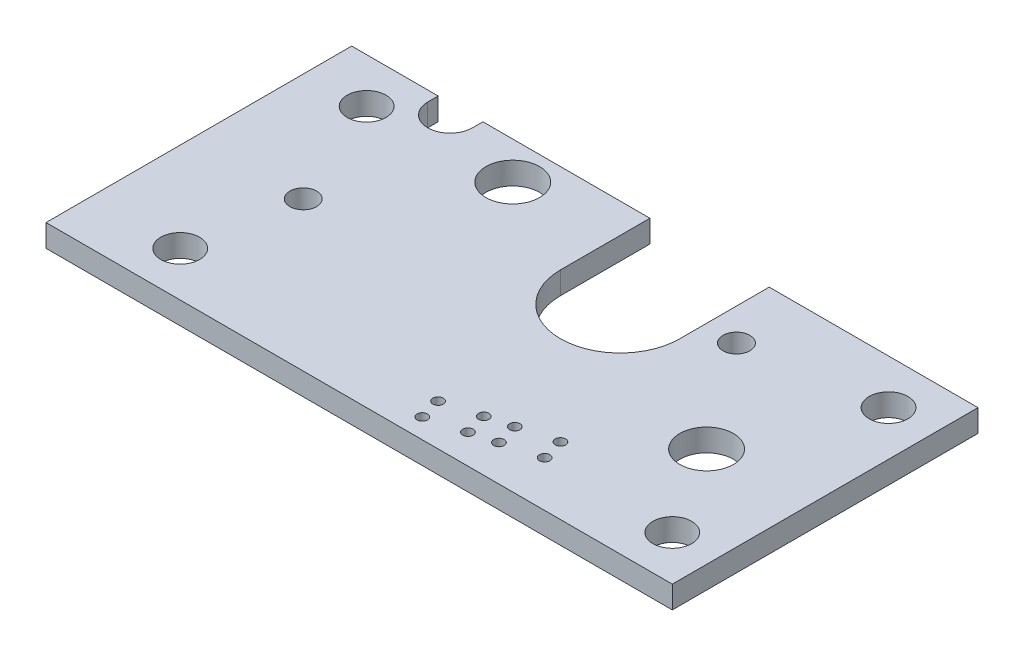
SolidWorks part; units mm, degrees
ref_plane "Спереди" through (0, 0, 0) normal (0, 0, 1) x (1, 0, 0)
ref_plane "Сверху" through (0, 0, 0) normal (0, 1, 0) x (1, 0, 0)
ref_plane "Справа" through (0, 0, 0) normal (1, 0, 0) x (0, 0, -1)
sketch "Эскиз1" plane through (0, 0, 0) normal (0, 1, 0) x (1, 0, 0)
  line L1 (0, 0) -> (42, 0)
  line L2 (0, 0) -> (0, 20.5)
  line L3 (0, 20.5) -> (42, 20.5)
  line L4 (42, 0) -> (42, 20.5)
  dimension "D1" = 42
  dimension "D2" = 20.5
extrude "Бобышка-Вытянуть1" add sketch "Эскиз1" along normal blind 1.5
sketch "Эскиз2" plane through (0, 1.5, 0) normal (0, 1, 0) x (1, 0, 0)
  line L0 (42, 20.5) -> (0, 20.5) construction
  line L1 (20, 14.5) -> (20, 20.5)
  line L2 (42, 0) -> (42, 20.5) construction
  line L3 (28, 14.5) -> (28, 20.5)
  line L4 (28, 20.5) -> (20, 20.5)
  circle A0 centre (24, 14.5) radius 4
  line M4 (42, 20.5) -> (0, 20.5)
  dimension "D2" = 18
  dimension "D3" = 8
  dimension "D1" = 6
extrude "Вырез-Вытянуть1" cut sketch "Эскиз2" against normal through all contours A0 | A0 L3 L1 M4
sketch "Эскиз4" plane through (0, 1.5, 0) normal (0, 1, 0) x (1, 0, 0)
  line L1 (0, 20.5) -> (0, 0) construction
  line L2 (5.8, 19.8) -> (5.8, 20.5)
  line L3 (42, 20.5) -> (28, 20.5) construction
  line L4 (8.8, 19.8) -> (8.8, 20.5)
  line L5 (8.8, 20.5) -> (5.8, 20.5)
  line L6 (0, 10.8735) -> (0, 7.1265)
  line L7 (42, 0) -> (42, 20.5) construction
  line L8 (0, 0) -> (42, 0) construction
  circle A0 centre (7.25, 10) radius 0.9
  circle A1 centre (30.15, 16.15) radius 0.9
  circle A4 centre (39, 3) radius 1.3
  circle A5 centre (39, 17.5) radius 1.3
  circle A6 centre (6, 3) radius 1.3
  circle A7 centre (4, 17.5) radius 1.3
  arc A8 (5.8, 19.8) -> (8.8, 19.8) centre (7.3, 19.8) ccw
  arc A9 (0, 7.1265) -> (0, 10.8735) centre (-0.7, 9) ccw
  circle A10 centre (13.3, 18) radius 1.8
  circle A13 centre (35.3, 9) radius 1.8
  arc A15 (20, 14.5) -> (28, 14.5) centre (24, 14.5) ccw construction
  dimension "D1" = 2
  dimension "D3" = 2.6
  dimension "D4" = 3.6
  dimension "D6" = 4
  dimension "D8" = 3
  dimension "D9" = 1.25
  dimension "D10" = 7
  dimension "D11" = 22.9
  dimension "D12" = 6.15
  dimension "D13" = 1.8
  dimension "D16" = 11.3
  dimension "D17" = 22
  dimension "D18" = 5.5
  dimension "D19" = 9
  dimension "D20" = 6
  dimension "D21" = 1.8
  dimension "D22" = 24.7
  dimension "D23" = 5.5
  dimension "D2" = 3
  dimension "D5" = 3
  dimension "D7" = 3
  dimension "D24" = 6
extrude "Вырез-Вытянуть3" cut sketch "Эскиз4" against normal up to next
sketch "Эскиз5" plane through (0, 1.5, 0) normal (0, 1, 0) x (1, 0, 0)
  line L0 (30.378, 3.061) -> (23.9063, 1.3269) construction
  line L1 (23.9063, 1.3269) -> (23.518, 2.7758) construction
  line L2 (23.518, 2.7758) -> (29.9897, 4.5099) construction
  line L3 (29.9897, 4.5099) -> (30.378, 3.061) construction
  line L4 (27.9631, 2.4139) -> (27.5749, 3.8628) construction
  line L5 (26.3211, 1.9739) -> (25.9328, 3.4228) construction
  line L6 (26.2002, 3.3909) -> (25.6655, 3.4547) construction
  line L7 (23.7336, 2.9371) -> (23.2507, 2.8077) construction
  circle A0 centre (29.9897, 4.5099) radius 0.35
  circle A1 centre (27.5749, 3.8628) radius 0.35
  circle A2 centre (25.9328, 3.4228) radius 0.35
  circle A3 centre (23.518, 2.7758) radius 0.35
  circle A4 centre (30.378, 3.061) radius 0.35
  circle A5 centre (27.9631, 2.4139) radius 0.35
  circle A6 centre (26.3211, 1.9739) radius 0.35
  circle A7 centre (23.9063, 1.3269) radius 0.35
  dimension "D1" = 0.7
  dimension "D2" = 1.5
  dimension "D3" = 2.5
  dimension "D4" = 2.5
  dimension "D5" = 1.7
extrude "Вырез-Вытянуть4" cut sketch "Эскиз5" against normal through all
